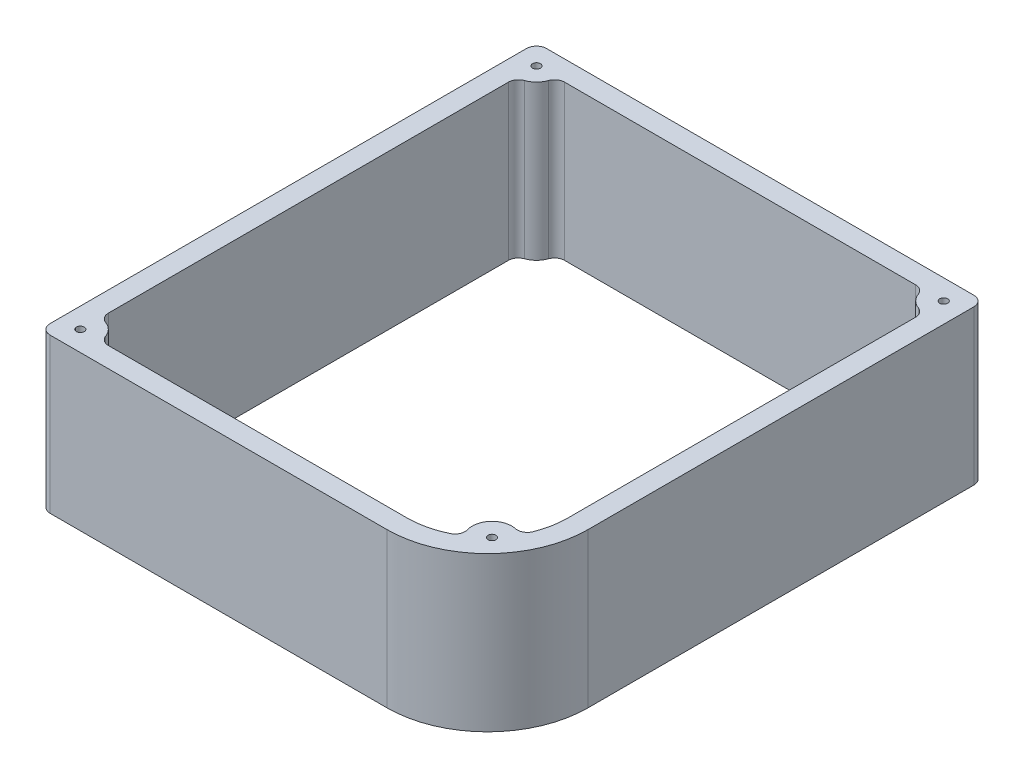
SolidWorks part; units mm, degrees
ref_plane "Front Plane" through (0, 0, 0) normal (0, 0, 1) x (1, 0, 0)
ref_plane "Top Plane" through (0, 0, 0) normal (0, 1, 0) x (1, 0, 0)
ref_plane "Right Plane" through (0, 0, 0) normal (1, 0, 0) x (0, 0, -1)
sketch "Sketch1" plane through (0, 0, 0) normal (0, 1, 0) x (1, 0, 0)
  line L0 (38.2045, 48.03) -> (-54.6555, 48.03)
  line L1 (-45.6855, 40.41) -> (29.2345, 40.41) construction
  line L2 (-45.6855, 40.41) -> (-45.6855, -59.5901) construction
  line L3 (-45.6855, -59.5901) -> (29.2345, -59.5901) construction
  line L4 (29.2345, 40.41) -> (29.2345, -59.5901) construction
  line L5 (48.2845, 53.11) -> (-64.7355, 53.11)
  line L6 (48.2845, 53.11) -> (48.2845, -46.8901)
  line L7 (22.8845, -72.2901) -> (-64.7355, -72.2901)
  line L8 (-64.7355, 53.11) -> (-64.7355, -72.2901)
  line L9 (-59.6555, 43.03) -> (-59.6555, -62.2101)
  line L10 (22.8845, -67.2101) -> (-54.6555, -67.2101)
  line L11 (43.2045, 43.03) -> (43.2045, -46.8901)
  line L12 (43.2045, 48.03) -> (-59.6555, 48.03) construction
  line L13 (-59.6555, 48.03) -> (-59.6555, -67.2101) construction
  line L14 (43.2045, 48.03) -> (43.2045, -46.8901) construction
  line L15 (22.8845, -67.2101) -> (-59.6555, -67.2101) construction
  line L16 (-54.6555, 48.03) -> (49945.3445, 48.03) construction
  line L17 (43.2045, 40.4991) -> (43.2045, -49959.5009) construction
  line L18 (-25.2243, -67.2101) -> (-50025.2243, -67.2101) construction
  line L19 (-59.6555, -48.2991) -> (-59.6555, -50048.2991) construction
  arc A0 (22.8845, -72.2901) -> (48.2845, -46.8901) centre (22.8845, -46.8901) ccw
  arc A1 (22.8845, -67.2101) -> (33.9996, -63.9006) centre (22.8845, -46.8901) ccw
  circle A2 centre (-59.6555, 48.03) radius 1
  arc A3 (-59.6555, 43.03) -> (-54.6555, 48.03) centre (-59.6555, 48.03) ccw
  arc A4 (38.2045, 48.03) -> (43.2045, 43.03) centre (43.2045, 48.03) ccw
  arc A5 (-54.6555, -67.2101) -> (-59.6555, -62.2101) centre (-59.6555, -67.2101) ccw
  arc A6 (40.7175, -56.631) -> (33.9996, -63.9006) centre (37.8809, -60.7485) ccw
  arc A7 (22.8845, -67.2101) -> (43.2045, -46.8901) centre (22.8845, -46.8901) ccw construction
  arc A8 (40.7175, -56.631) -> (43.2045, -46.8901) centre (22.8845, -46.8901) ccw
  circle A9 centre (43.2045, 48.03) radius 1
  circle A10 centre (-59.6555, -67.2101) radius 1
  circle A11 centre (37.8809, -60.7485) radius 1
  dimension "D3" = 50.8
  dimension "D7" = 25.4
  dimension "D8" = 25.4
  dimension "D9" = 5.08
  dimension "D10" = 2
  dimension "D11" = 10
  dimension "D12" = 2
  dimension "D13" = 5
  dimension "D14" = 5
  dimension "D15" = 2
  dimension "D16" = 2
  dimension "D17" = 5
  dimension "D1" = 100.0001
  dimension "D2" = 74.92
  dimension "0.75" = 19.05
  dimension "D4" = 19.05
  dimension "D5" = 12.7
  dimension "D6" = 12.7
extrude "Boss-Extrude3" add sketch "Sketch1" along normal blind 39
fillet "Fillet1" radius 2.54 11 edges at (-64.7355, 19.5, 72.2901) (-64.7355, 19.5, -53.11) (48.2845, 19.5, -53.11) (-59.6555, 19.5, 62.2101) (-54.6555, 19.5, 67.2101) (33.9996, 19.5, 63.9006) (40.7175, 19.5, 56.631) (43.2045, 19.5, -43.03) (38.2045, 19.5, -48.03) (-54.6555, 19.5, -48.03) (-59.6555, 19.5, -43.03)
